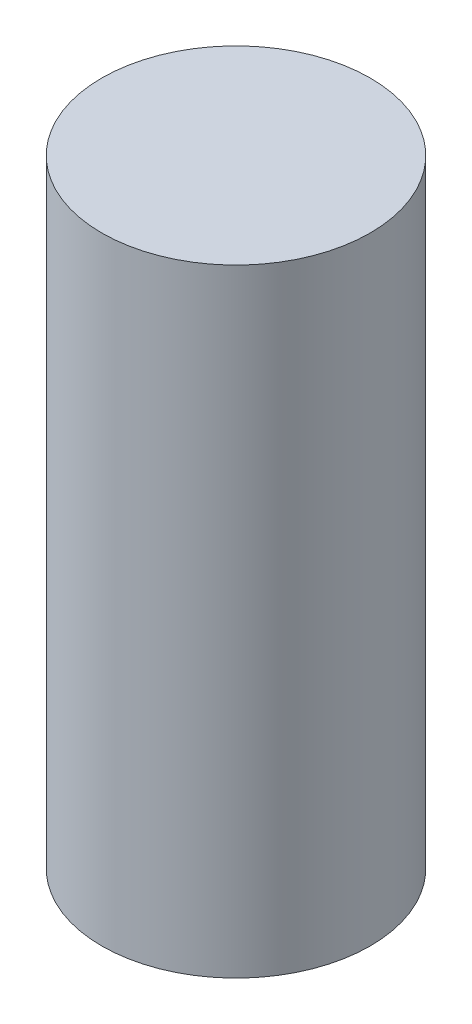
SolidWorks part; units mm, degrees
ref_plane "Спереди" through (0, 0, 0) normal (0, 0, 1) x (1, 0, 0)
ref_plane "Сверху" through (0, 0, 0) normal (0, 1, 0) x (1, 0, 0)
ref_plane "Справа" through (0, 0, 0) normal (1, 0, 0) x (0, 0, -1)
sketch "Эскиз1" plane through (0, 0, 0) normal (0, 1, 0) x (1, 0, 0)
  circle A0 centre (0, 0) radius 10
  dimension "D1" = 20
extrude "Бобышка-Вытянуть1" add sketch "Эскиз1" along normal blind 46
